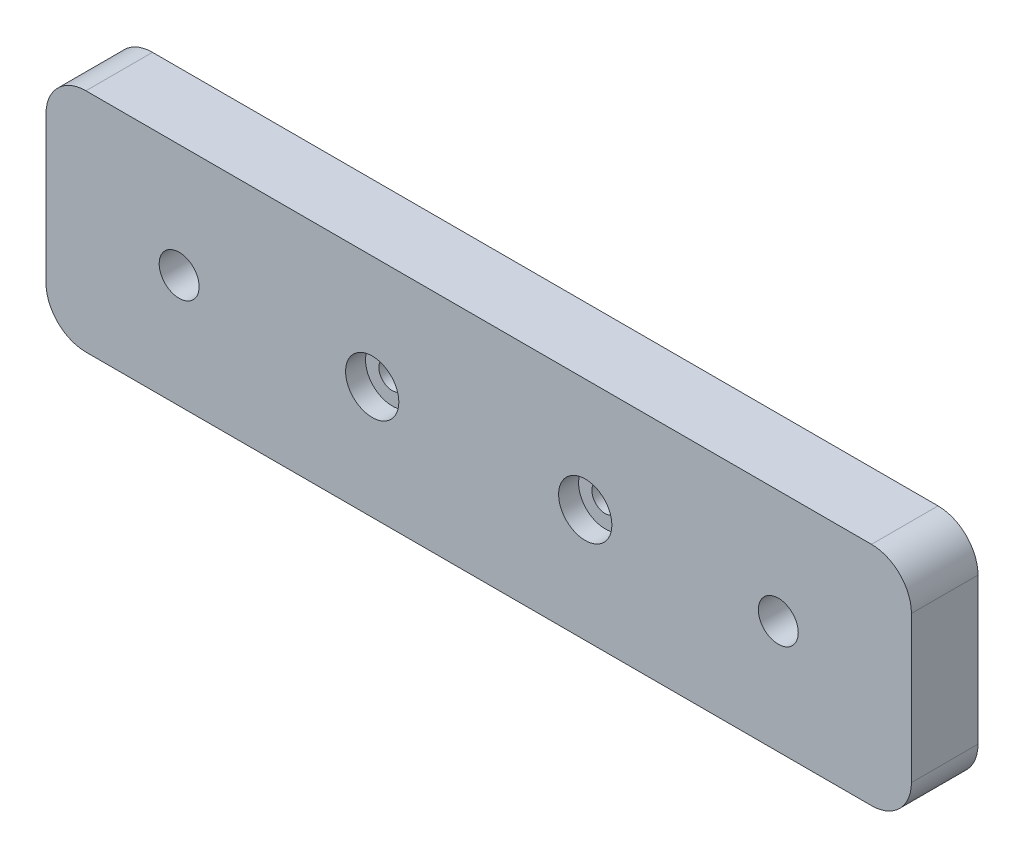
SolidWorks part; units mm, degrees
ref_plane "Front Plane" through (0, 0, 0) normal (0, 0, 1) x (1, 0, 0)
ref_plane "Top Plane" through (0, 0, 0) normal (0, 1, 0) x (1, 0, 0)
ref_plane "Right Plane" through (0, 0, 0) normal (1, 0, 0) x (0, 0, -1)
sketch "Sketch1" plane through (0, 0, 0) normal (0, 0, 1) x (1, 0, 0)
  line L0 (65, 8.5) -> (0, 8.5) construction
  line L1 (0, 0) -> (65, 0)
  line L2 (0, 0) -> (0, 17)
  line L3 (0, 17) -> (65, 17)
  line L4 (65, 0) -> (65, 17)
  line L5 (32.5, 17) -> (32.5, 0) construction
  circle A0 centre (55, 8.5) radius 1.5
  circle A1 centre (10, 8.5) radius 1.5
  circle A2 centre (24.5, 8.5) radius 1
  circle A3 centre (40.5, 8.5) radius 1
  dimension "D3" = 22.5
  dimension "D5" = 3
  dimension "D8" = 2
  dimension "D1" = 17
  dimension "D2" = 65
  dimension "D4" = 22.5
  dimension "D6" = 8
  dimension "D7" = 8
extrude "Boss-Extrude1" add sketch "Sketch1" along normal blind 5
fillet "Fillet1" radius 3 4 edges at (65, 17, 2.5) (65, 0, 2.5) (0, 0, 2.5) (0, 17, 2.5)
sketch "Sketch3" plane through (0, 0, 5) normal (0, 0, 1) x (1, 0, 0)
  circle A0 centre (24.5, 8.5) radius 2
  circle A1 centre (40.5, 8.5) radius 2
  dimension "D1" = 4
extrude "Cut-Extrude2" cut sketch "Sketch3" against normal blind 1.5
sketch "Sketch4" plane through (0, 0, 0) normal (0, 0, -1) x (-1, 0, 0)
  circle A0 centre (-55, 8.5) radius 3
  circle A1 centre (-10, 8.5) radius 3
  dimension "D1" = 6
extrude "Cut-Extrude3" cut sketch "Sketch4" against normal blind 2
